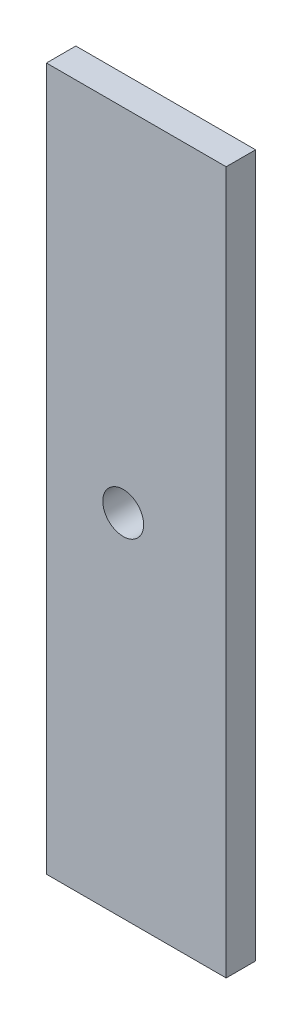
SolidWorks part; units mm, degrees
material "Balsa"
ref_plane "Front Plane" through (0, 0, 0) normal (0, 0, 1) x (1, 0, 0)
ref_plane "Top Plane" through (0, 0, 0) normal (0, 1, 0) x (1, 0, 0)
ref_plane "Right Plane" through (0, 0, 0) normal (1, 0, 0) x (0, 0, -1)
sketch "Sketch1" plane through (0, 0, 0) normal (0, 0, 1) x (1, 0, 0)
  line L1 (-55, 215) -> (55, 215)
  line L2 (-55, 215) -> (-55, -215)
  line L3 (-55, -215) -> (55, -215)
  line L4 (55, 215) -> (55, -215)
  line L5 (-55, 215) -> (55, -215) construction
  line L6 (-55, -215) -> (55, 215) construction
  circle A0 centre (-8, 0) radius 12.5
  point P0 (0, 0)
  point P20 (0, 215)
  dimension "D3" = 25
  dimension "D1" = 110
  dimension "D2" = 430
  dimension "D4" = 215
  dimension "D5" = 63
extrude "Boss-Extrude1" add sketch "Sketch1" along normal blind 18
